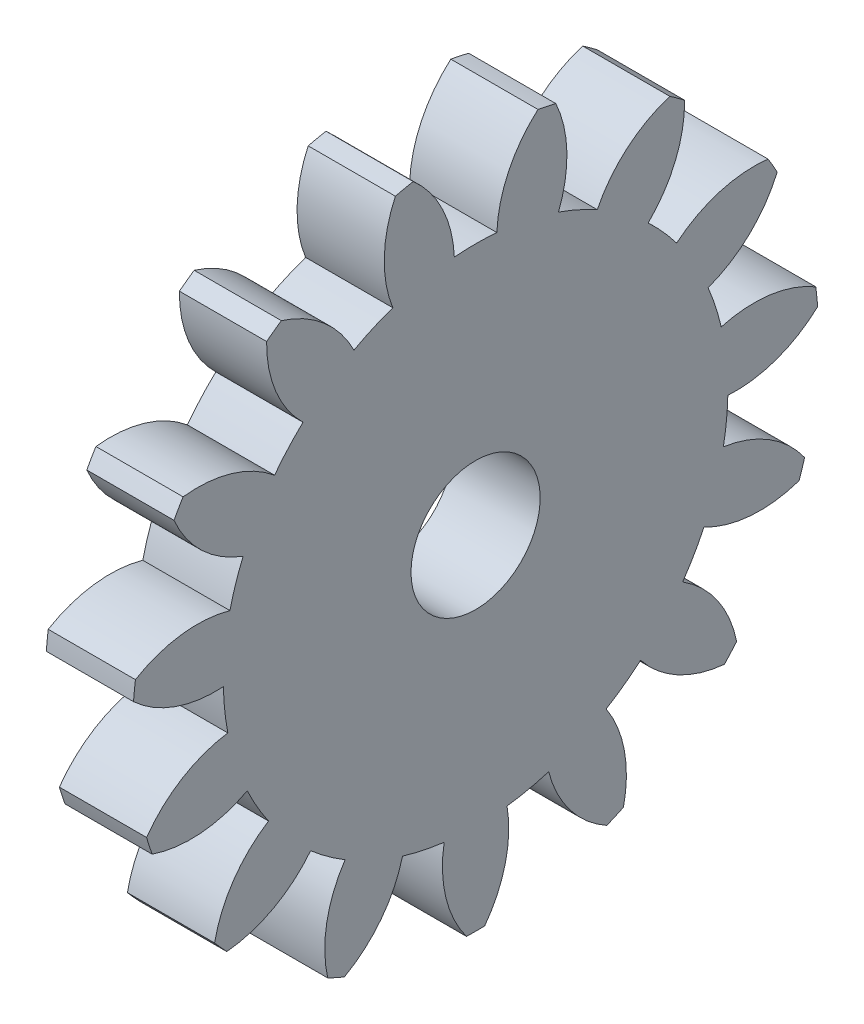
SolidWorks part; units mm, degrees
ref_plane "Plane1" through (0, 0, 0) normal (0, 0, 1) x (1, 0, 0)
ref_plane "Plane2" through (0, 0, 0) normal (0, 1, 0) x (1, 0, 0)
ref_plane "Plane3" through (0, 0, 0) normal (1, 0, 0) x (0, 0, -1)
other "Configuration Table"
sketch "HoldingSke" plane through (0, 0, 0) normal (0, 1, 0) x (1, 0, 0)
  line L0 (0, 0) -> (0.3864, -0.1035)
  line L1 (-15, 0) -> (100, 0) construction
  line L2 (0, 0) -> (-2.1039, 2.3779)
  line L3 (0, 0) -> (-11.863, 4.5341)
  line L4 (0, 0) -> (8.3417, 2.2352)
  line L5 (0, 0) -> (-46.8476, -17.4728)
  line L6 (0, 0) -> (-4.4764, -3.0202)
  line L7 (-2.1039, 2.3779) -> (8.6586, 51.2059)
  line L8 (-76.2, 54.61) -> (-74.8, 54.61)
  line L9 (-71.009, 38.7566) -> (-53.1078, 45.2721)
  line L10 (-76.2, 71.12) -> (104.1128, 71.12)
  line L11 (0, 0) -> (-5.4, 0)
  line L12 (-76.2, 101.6) -> (-76.113, 101.6)
  line L13 (24.9733, 27.94) -> (52.9518, 28.4284)
  line L14 (24.9733, 27.94) -> (24.9743, 27.94)
  line L15 (24.9733, 27.94) -> (100.4006, 29.5858)
  line L16 (-63.627, -2.5) -> (-12.827, -2.5)
  circle A0 centre (0, 0) radius 4
  circle A1 centre (0, 0) radius 15.624
  circle A2 centre (0, 0) radius 37.5
  circle A3 centre (0, 0) radius 4
  dimension "MHD" = 31.248
  dimension "Hub_dia" = 75
  dimension "Bore" = 8
  dimension "MBD" = 8
  dimension "Num_teeth" = 15
  dimension "Pitch" = 0.4
  dimension "Overall_len" = 50
  dimension "Show_teeth" = 15
  dimension "Thickness" = 5.4
  dimension "OAL" = 50.0001
  dimension "T_dim" = 1.4
  dimension "Ap" = 20
  dimension "H" = 19.05
  dimension "Pitch_radius" = 180.3128
  dimension "Width" = 5.4
  dimension "Backlash" = 0.087
  dimension "Addendum_fac" = 1
  dimension "Dedendum_fac" = 1.25
  dimension "Clearance_fac" = 0.25
  dimension "Dedendum_add" = 0.001
  dimension "Module" = 2.5
sketch "BasProSke" plane through (0, 0, 0) normal (0, 1, 0) x (1, 0, 0)
  line L0 (-10, 0) -> (60, 0) construction
  line L1 (0, 0) -> (0, 21.25)
  line L2 (0, 0) -> (5.4, 0)
  line L3 (5.4, 0) -> (5.4, 21.25)
  line L4 (5.4, 21.25) -> (0, 21.25)
  dimension "Thickness" = 5.4
  dimension "Diameter" = 42.5
revolve "Base-Revolve" add sketch "BasProSke" angle 360 about L0
sketch "TooCutSke" plane through (0, 0, 0) normal (1, 0, 0) x (0, 0, -1)
  line L1 (0, 0) -> (0, 107) construction
  line L2 (0, 0) -> (-2.112, 18.6307) construction
  line L3 (0, 0) -> (-7.7604, 36.5097) construction
  line L4 (-2.112, 18.6307) -> (-3.8802, 18.2548) construction
  arc A0 (1.3173, 15.5684) -> (-1.3173, 15.5684) centre (0, 0) ccw
  arc A1 (3.8889, 20.917) -> (-3.8889, 20.917) centre (0, 0) ccw
  circle A2 centre (0, 0) radius 18.75 construction
  circle A3 centre (0, 0) radius 17.6192 construction
  arc A4 (-1.3173, 15.5684) -> (-3.8889, 20.917) centre (-8.8109, 15.258) ccw
  arc A5 (3.8889, 20.917) -> (1.3173, 15.5684) centre (8.8109, 15.258) ccw
  dimension "Root_dia" = 31.248
  dimension "Overcut_dia" = 42.5508
  dimension "Pitch_dia" = 37.5
  dimension "Base_dia" = 35.2385
  dimension "Flank_rad" = 7.5
  dimension "Half_ang" = 12
  dimension "Half_CT" = 1.8077
extrude "ToothCut" cut sketch "TooCutSke" along normal through all
fillet "Breaks" [suppressed] radius 0.05
fillet "RootFillets" [suppressed] radius 0.626
pattern_circular "TeethCuts" count 15 every 24 about axis through (-10, 0, 0) along (1, 0, 0) of "ToothCut", "RootFillets", "Breaks"
sketch "HubNeaOneSke" plane through (0, 0, 0) normal (-1, 0, 0) x (0, 0, 1)
  circle A0 centre (0, 0) radius 15.624
  dimension "Diameter" = 31.248
extrude "HubNearOne" [suppressed] add sketch "HubNeaOneSke" along normal blind 44.6001
sketch "HubNeaBotSke" plane through (0, 0, 0) normal (-1, 0, 0) x (0, 0, 1)
  circle A0 centre (0, 0) radius 15.624
  dimension "Diameter" = 31.248
extrude "HubNearBoth" [suppressed] add sketch "HubNeaBotSke" along normal blind 22.3
ref_plane "FarPln" through (5.4, 0, 0) normal (1, 0, 0) x (0, 0, -1)
sketch "HubFarSke" plane through (5.4, 0, 0) normal (1, 0, 0) x (0, 0, -1)
  circle A0 centre (0, 0) radius 15.624
  dimension "Diameter" = 31.248
extrude "HubFar" [suppressed] add sketch "HubFarSke" along normal blind 22.3
sketch "BorSke" plane through (0, 0, 0) normal (1, 0, 0) x (0, 0, -1)
  circle A0 centre (0, 0) radius 4
  dimension "Diameter" = 8
extrude "Bore" cut sketch "BorSke" along normal mid plane 100.0001
sketch "KeySke" plane through (0, 0, 0) normal (1, 0, 0) x (0, 0, -1)
  line L0 (-1.5, 0) -> (-1.5, 5.4)
  line L1 (-1.5, 5.4) -> (1.5, 5.4)
  line L2 (1.5, 5.4) -> (1.5, 0)
  line L3 (0, 0) -> (0, 34) construction
  line L4 (-1.5, 0) -> (1.5, 0)
  dimension "Offset" = 5.4
  dimension "Width" = 3
extrude "Keyway" [suppressed] cut sketch "KeySke" along normal mid plane 100.0001
pattern_circular "Keyway2" [suppressed] count 2 every 90 about axis through (-10, 0, 0) along (1, 0, 0)
equation "' \"Module@HoldingSke\" = 6.35"
equation "' \"Num_teeth@HoldingSke\" = 12"
equation "' \"Ap@HoldingSke\" =  20"
equation "' \"Ap@HoldingSke\" = 20"
equation "' \"Width@HoldingSke\" = 0.5 * 25.4"
equation "' \"Hub_dia@HoldingSke\"= 1 * 25.4"
equation "' \"Hub_dia@HoldingSke\" = 1 * 25.4"
equation "' \"Overall_len@HoldingSke\" = 1.0 * 25.4"
equation "' \"Bore@HoldingSke\" = 0.75 * 25.4"
equation "' \"T_dim@HoldingSke\" = 0.1 * 25.4"
equation "' \"Width@KeySke\" = 0.25 * 25.4"
equation "' \"Show_teeth@HoldingSke\" = 13"
equation "' \"Backlash@HoldingSke\" = 0.009 * 25.4"
equation "' \"Addendum_fac@HoldingSke\" = 1.0"
equation "' \"Dedendum_fac@HoldingSke\" = 1.25"
equation "' \"Dedendum_add@HoldingSke\" = 0.00005 * 25.4"
equation "' \"Clearance_fac@HoldingSke\" = 0.25"
equation "\"Pitch@HoldingSke\" = 1 / \"Module@HoldingSke\""
equation "\"Overcut_dia@TooCutSke\" = (\"Num_teeth@HoldingSke\" + 2 * \"Addendum_fac@HoldingSke\") / \"Pitch@HoldingSke\" + 0.002 * 25.4"
equation "\"Pitch_dia@TooCutSke\" = \"Num_teeth@HoldingSke\" / \"Pitch@HoldingSke\""
equation "\"Base_dia@TooCutSke\" = \"Num_teeth@HoldingSke\" / \"Pitch@HoldingSke\" * cos((\"Ap@HoldingSke\"  * 3.14159265 / 180))"
equation "\"Root_dia@TooCutSke\" = (\"Num_teeth@HoldingSke\" + 2) / \"Pitch@HoldingSke\" - 2 * (\"Addendum_fac@HoldingSke\" + \"Dedendum_fac@HoldingSke\") / \"Pitch@HoldingSke\" - \"Dedendum_add@HoldingSke\" * 2"
equation "\"Half_ang@TooCutSke\" = 180 / \"Num_teeth@HoldingSke\""
equation "\"Half_CT@TooCutSke\" = \"Num_teeth@HoldingSke\" / \"Pitch@HoldingSke\" * sin((3.14159265 / 2 / \"Num_teeth@HoldingSke\")) / 2 - 7 * \"Backlash@HoldingSke\" / 4"
equation "\"Flank_rad@TooCutSke\" = \"Num_teeth@HoldingSke\" / \"Pitch@HoldingSke\" / 5"
equation "\"Radius@RootFillets\" = \"Clearance_fac@HoldingSke\" / \"Pitch@HoldingSke\" + \"Dedendum_add@HoldingSke\""
equation "\"Break_rad@Breaks\" = 0.02 / \"Pitch@HoldingSke\""
equation "\"Thickness@HoldingSke\" = \"Width@HoldingSke\""
equation "\"OAL@HoldingSke\" = \"Thickness@HoldingSke\""
equation "\"MHD@HoldingSke\" = (\"Num_teeth@HoldingSke\" + 2) / \"Pitch@HoldingSke\" - 2 * (\"Addendum_fac@HoldingSke\" + \"Dedendum_fac@HoldingSke\")  / \"Pitch@HoldingSke\" - \"Dedendum_add@HoldingSke\" * 2"
equation "\"MBD@HoldingSke\" = (\"Num_teeth@HoldingSke\" + 2) / \"Pitch@HoldingSke\" - 2 * (\"Addendum_fac@HoldingSke\" + \"Dedendum_fac@HoldingSke\")  / \"Pitch@HoldingSke\" - \"Dedendum_add@HoldingSke\" * 2 - 0.002 * 25.4"
equation "\"MHD@HoldingSke\" = ((sgn( \"MHD@HoldingSke\" - \"Hub_dia@HoldingSke\" )-1)*( \"MHD@HoldingSke\" - \"Hub_dia@HoldingSke\" ))/-2+ \"Hub_dia@HoldingSke\""
equation "\"MBD@HoldingSke\" = ((sgn( \"MBD@HoldingSke\" - \"Bore@HoldingSke\" )-1)*( \"MBD@HoldingSke\" - \"Bore@HoldingSke\" ))/-2+ \"Bore@HoldingSke\""
equation "\"OAL@HoldingSke\" = ((sgn( \"OAL@HoldingSke\" - \"Overall_len@HoldingSke\" )+1)*( \"OAL@HoldingSke\" - \"Overall_len@HoldingSke\" ))/2 + \"Overall_len@HoldingSke\" + 0.000002 * 25.4"
equation "\"Num_teeth@TeethCuts\" = int( \"Show_teeth@HoldingSke\" ) + 1"
equation "\"Num_teeth@TeethCuts\" = ((sgn( \"Num_teeth@TeethCuts\" - \"Num_teeth@HoldingSke\" )-1)*( \"Num_teeth@TeethCuts\" - \"Num_teeth@HoldingSke\" ))/-2+ \"Num_teeth@HoldingSke\""
equation "\"Num_teeth@TeethCuts\" = ((sgn( \"Num_teeth@TeethCuts\" - 2.0)+1)*( \"Num_teeth@TeethCuts\" - 2.0))/2 +2.0"
equation "\"Angle@TeethCuts\" = 360.0 / \"Num_teeth@HoldingSke\""
equation "\"Diameter@BasProSke\" = (\"Num_teeth@HoldingSke\" + 2 * \"Addendum_fac@HoldingSke\") / \"Pitch@HoldingSke\""
equation "\"Thickness@BasProSke\"  = \"Thickness@HoldingSke\""
equation "' \"Fillet_rad@BasProSke\" =  \"Thickness@HoldingSke\" * 0.05"
equation "' \"Fillet_rad@BasProSke\" = \"Thickness@HoldingSke\" * 0.05"
equation "\"MHD@HoldingSke\" = ((sgn( \"MHD@HoldingSke\" - \"Root_dia@TooCutSke\" )-1)*( \"MHD@HoldingSke\" - \"Root_dia@TooCutSke\" ))/-2+ \"Root_dia@TooCutSke\""
equation "\"Diameter@HubNeaOneSke\" = \"MHD@HoldingSke\""
equation "\"Length@HubNearOne\" = \"OAL@HoldingSke\" - \"Thickness@BasProSke\""
equation "\"Diameter@HubNeaBotSke\" = \"MHD@HoldingSke\""
equation "\"Length@HubNearBoth\" = ( \"OAL@HoldingSke\" - \"Thickness@BasProSke\" ) / 2.0"
equation "\"Thickness@FarPln\" = \"Thickness@BasProSke\""
equation "\"Diameter@HubFarSke\" = \"MHD@HoldingSke\""
equation "\"Length@HubFar\" = ( \"OAL@HoldingSke\" - \"Thickness@BasProSke\" ) / 2.0"
equation "\"Diameter@BorSke\" = \"MBD@HoldingSke\""
equation "\"D1@Bore\" = \"OAL@HoldingSke\" * 2.0"
equation "\"D1@Keyway\" = \"OAL@HoldingSke\" * 2.0"
equation "\"Offset@KeySke\" = \"T_dim@HoldingSke\" + \"MBD@HoldingSke\" / 2.0"
